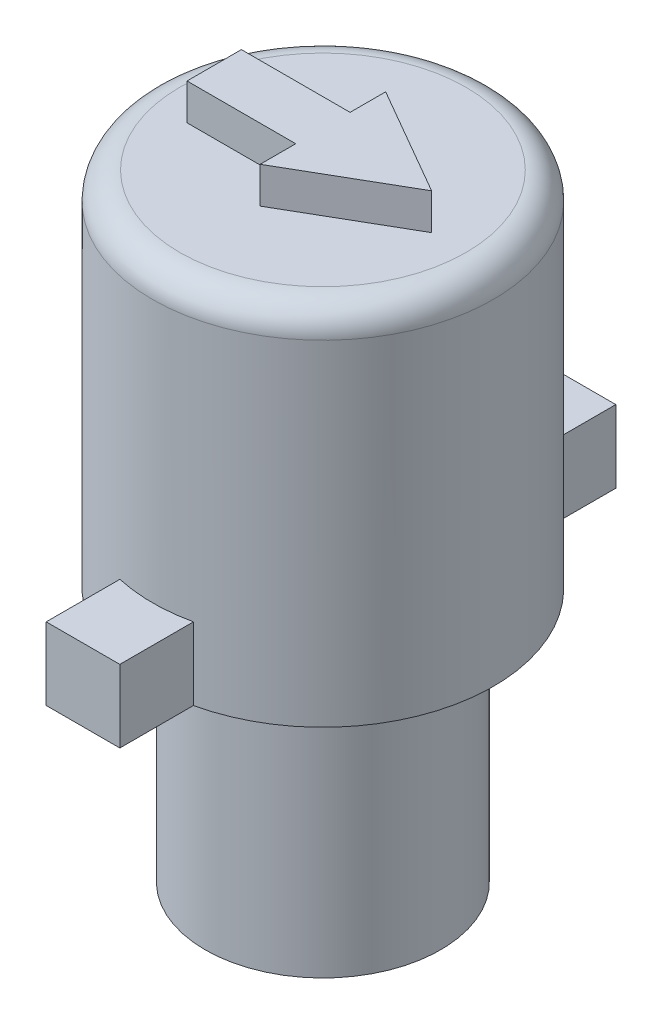
SolidWorks part; units mm, degrees
ref_plane "Front Plane" through (0, 0, 0) normal (0, 0, 1) x (1, 0, 0)
ref_plane "Top Plane" through (0, 0, 0) normal (0, 1, 0) x (1, 0, 0)
ref_plane "Right Plane" through (0, 0, 0) normal (1, 0, 0) x (0, 0, -1)
sketch "Sketch1" plane through (0, 0, 0) normal (0, 1, 0) x (1, 0, 0)
  circle A0 centre (0, 0) radius 3.25
  dimension "D1" = 6.5
extrude "Boss-Extrude1" add sketch "Sketch1" along normal blind 7.018 contours A0
sketch "Sketch2" plane through (0, 0, 0) normal (0, -1, 0) x (1, 0, 0)
  circle A1 centre (0, 0) radius 1.75
  dimension "D1" = 3.5
extrude "Cut-Extrude1" [suppressed] cut sketch "Sketch2" against normal blind 2.5
sketch "Sketch6" plane through (0, 7.018, 0) normal (0, 1, 0) x (1, 0, 0)
  circle A0 centre (0, 0) radius 4.7
  dimension "D1" = 9.4
extrude "Boss-Extrude2" add sketch "Sketch6" along normal blind 10 contours A0
fillet "Fillet1" radius 0.75 1 edges at (0, 17.018, 4.7)
sketch "Sketch7" plane through (0, 17.018, 0) normal (0, 1, 0) x (1, 0, 0)
  line L0 (0, 0) -> (-3, 0) construction
  line L1 (0, 0) -> (1, 0) construction
  line L2 (0, 0) -> (1, 0) construction
  line L3 (3, 0) -> (0, 1.7321)
  line L4 (0, 1.7321) -> (0, -1.7321)
  line L5 (0, -1.7321) -> (3, 0)
  line L6 (1, 0) -> (3, 0) construction
  line L7 (-3, 0) -> (-3, 0.75)
  line L8 (-3, 0.75) -> (0, 0.75)
  line L9 (0, 0.75) -> (0, -0.75)
  line L10 (0, -0.75) -> (-3, -0.75)
  line L11 (-3, -0.75) -> (-3, 0)
  circle A0 centre (1, 0) radius 1 construction
  dimension "D1" = 1
  dimension "D2" = 2
  dimension "D3" = 3
  dimension "D4" = 0.75
  dimension "D5" = 0.75
sketch "Sketch8" plane through (0, 17.018, 0) normal (0, 1, 0) x (1, 0, 0)
  line L0 (0, 0.75) -> (-3, 0.75)
  line L1 (-3, 0.75) -> (-3, -0.75)
  line L2 (-3, -0.75) -> (0, -0.75)
  line L3 (0, -0.75) -> (0, -1.7321)
  line L4 (0, -1.7321) -> (3, 0)
  line L5 (3, 0) -> (0, 1.7321)
  line L6 (0, 1.7321) -> (0, 0.75)
extrude "Boss-Extrude3" add sketch "Sketch8" along normal blind 1
sketch "Sketch9" plane through (0, 7.018, 0) normal (0, -1, 0) x (1, 0, 0)
  line L0 (0, 4.7) -> (0, -4.7) construction
  line L7 (-1.016, 4.5889) -> (-1.016, 6.6209)
  line L8 (-1.016, 6.6209) -> (1.016, 6.6209)
  line L9 (1.016, 6.6209) -> (1.016, 4.5889)
  line L10 (-1.651, -4.4005) -> (-1.651, -6.4325)
  line L11 (-1.651, -6.4325) -> (1.651, -6.4325)
  line L12 (1.651, -6.4325) -> (1.651, -4.4005)
  circle A1 centre (0, 0) radius 4.7 construction
  arc A3 (-1.651, -4.4005) -> (1.651, -4.4005) centre (0, 0) ccw
  arc A4 (1.016, 4.5889) -> (-1.016, 4.5889) centre (0, 0) ccw
  dimension "D2" = 2.032
  dimension "D3" = 3.302
  dimension "D4" = 2.032
  dimension "D1" = 2.032
extrude "Boss-Extrude4" add sketch "Sketch9" against normal blind 2
